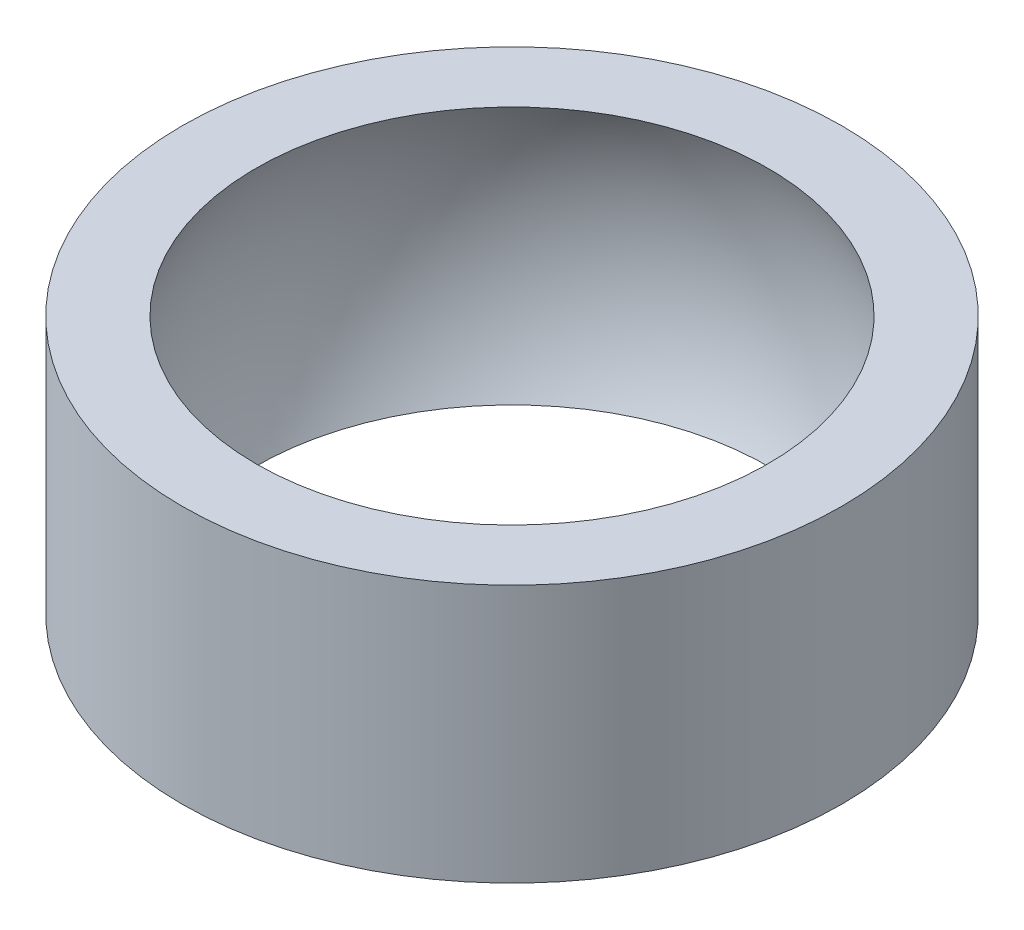
SolidWorks part; units mm, degrees
ref_plane "Front Plane" through (0, 0, 0) normal (0, 0, 1) x (1, 0, 0)
ref_plane "Top Plane" through (0, 0, 0) normal (0, 1, 0) x (1, 0, 0)
ref_plane "Right Plane" through (0, 0, 0) normal (1, 0, 0) x (0, 0, -1)
sketch "Sketch1" plane through (0, 0, 0) normal (0, 1, 0) x (1, 0, 0)
  circle A0 centre (0, 0) radius 8.5
  circle A1 centre (0, 0) radius 11.5
  dimension "D1" = 17
  dimension "D2" = 23
extrude "Boss-Extrude1" add sketch "Sketch1" along normal blind 9
sketch "Sketch2" plane through (0, 0, 0) normal (0, 0, 1) x (1, 0, 0)
  line L0 (0, 0) -> (0, 9) construction
  line L1 (8.5, 9) -> (-8.5, 9) construction
  line L2 (0, -5.5) -> (0, 14.5)
  line L3 (-17.1278, 4.5) -> (19.6579, 4.5) construction
  arc A0 (0, 14.5) -> (0, -5.5) centre (0, 4.5) cw
  point P10 (0, 4.5)
  dimension "D1" = 10
revolve "Cut-Revolve2" cut sketch "Sketch2" angle 360 about L2
